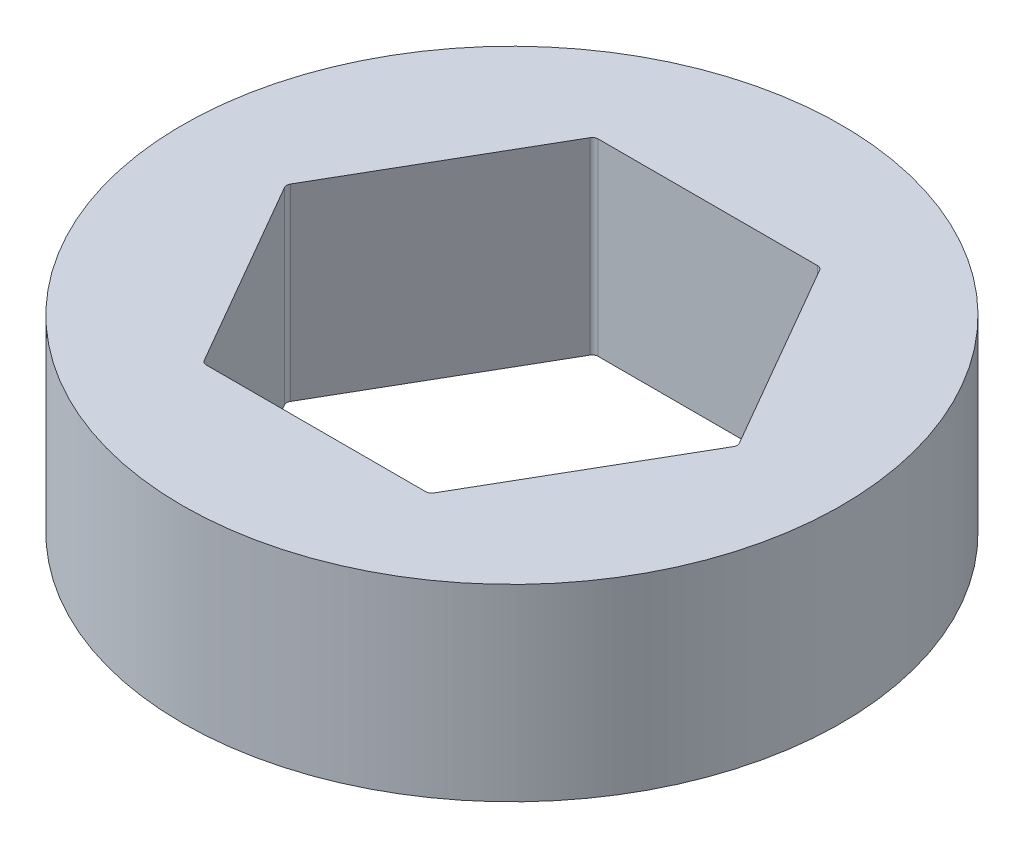
SolidWorks part; units mm, degrees
material "Nylon 101"
ref_plane "Front Plane" through (0, 0, 0) normal (0, 0, 1) x (1, 0, 0)
ref_plane "Top Plane" through (0, 0, 0) normal (0, 1, 0) x (1, 0, 0)
ref_plane "Right Plane" through (0, 0, 0) normal (1, 0, 0) x (0, 0, -1)
sketch "Sketch1" plane through (0, 0, 0) normal (0, 1, 0) x (1, 0, 0)
  line L1 (7.6256, 0) -> (3.8128, 6.604)
  line L2 (3.8128, 6.604) -> (-3.8128, 6.604)
  line L3 (-3.8128, 6.604) -> (-7.6256, 0)
  line L4 (-7.6256, 0) -> (-3.8128, -6.604)
  line L5 (-3.8128, -6.604) -> (3.8128, -6.604)
  line L6 (3.8128, -6.604) -> (7.6256, 0)
  circle A0 centre (0, 0) radius 11.1125
  circle A1 centre (0, 0) radius 6.604 construction
  dimension "D1" = 13.208
  dimension "D2" = 22.225
extrude "Boss-Extrude1" add sketch "Sketch1" along normal blind 6.35
fillet "Fillet1" radius 0.2 6 edges at (3.8128, 3.175, -6.604) (-3.8128, 3.175, -6.604) (-7.6256, 3.175, 0) (3.8128, 3.175, 6.604) (7.6256, 3.175, 0) (-3.8128, 3.175, 6.604)
